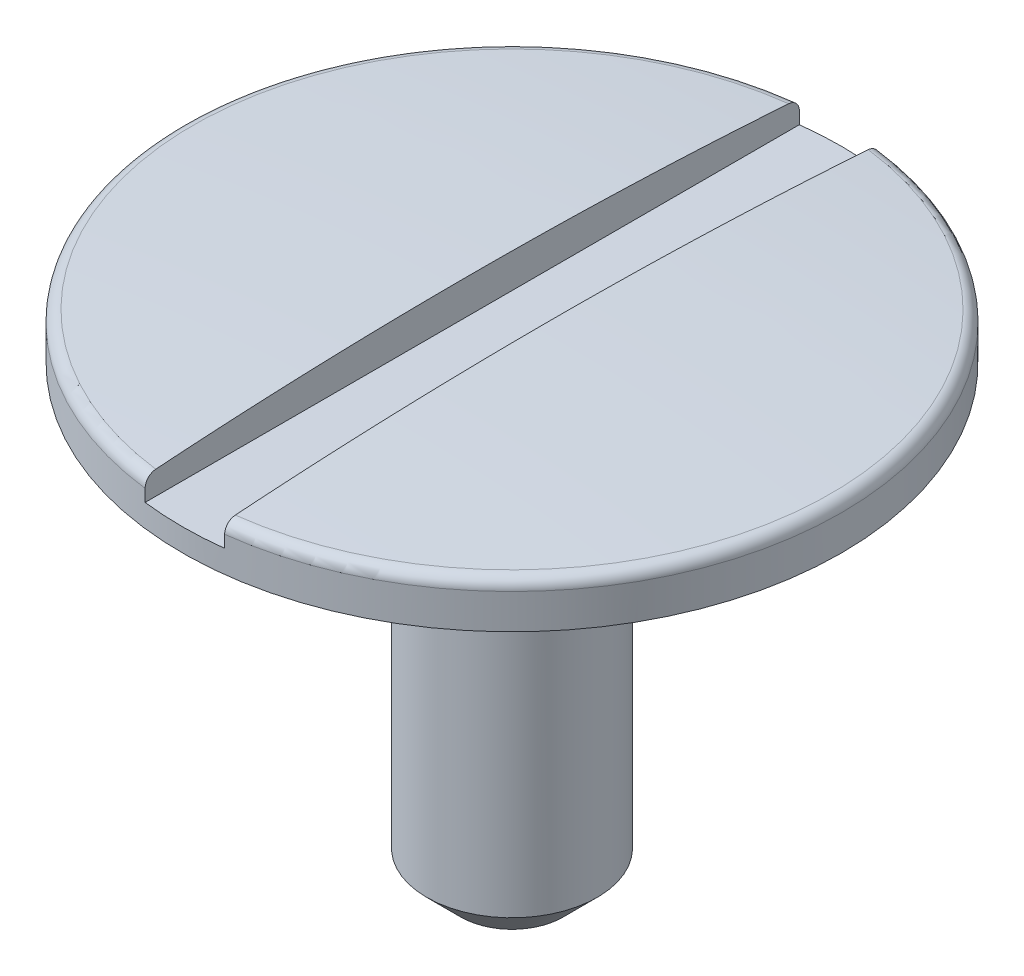
SolidWorks part; units mm, degrees
ref_plane "Alzado" through (0, 0, 0) normal (0, 0, 1) x (1, 0, 0)
ref_plane "Planta" through (0, 0, 0) normal (0, 1, 0) x (1, 0, 0)
ref_plane "Vista lateral" through (0, 0, 0) normal (1, 0, 0) x (0, 0, -1)
sketch "Sketch4" plane through (0, 0, 0) normal (0, 0, 1) x (1, 0, 0)
  line L0 (-848.3562, 0) -> (41569.4551, 0) construction
  line L1 (-848.2787, 0.2) -> (41569.5327, 0.2) construction
  line L2 (0, -848.3562) -> (0, 41569.4551) construction
  line L3 (1.45, -848.3562) -> (1.45, 41569.4551) construction
  line L4 (0, 0) -> (1.45, 0)
  line L5 (1.45, 0) -> (1.45, 0.2)
  line L6 (0, 0.2526) -> (0, 0)
  arc A1 (0, 0.2526) -> (1.45, 0.2) centre (0, -19.7474) cw
  point P8 (1.45, 0.2)
  dimension "D3" = 20
  dimension "D1" = 1.45
  dimension "D2" = 0.2
revolve "Revolve1" add sketch "Sketch4" angle 360 about L2
sketch "Sketch2" plane through (0, 0, 0) normal (0, 1, 0) x (1, 0, 0)
  circle A0 centre (0, 0) radius 0.375
  dimension "D1" = 0.75
extrude "Boss-Extrude2" add sketch "Sketch2" against normal blind 2
fillet "Fillet1" radius 0.05 1 edges at (1.45, 0.2, 0)
chamfer "Chamfer2" distance 0.15 angle 45 1 edges at (0, -2, 0.375)
sketch "Sketch3" plane through (0, 0, 0) normal (0, 0, 1) x (1, 0, 0)
  line L0 (0, -1000) -> (0, 49000) construction
  line L2 (-0.175, -999.9073) -> (-0.175, 49000.0927) construction
  line L3 (-1000, 0) -> (49000, 0) construction
  line L4 (-1000.8273, 0.1) -> (48999.1727, 0.1) construction
  line L5 (-0.175, 0.35) -> (0, 0.35)
  line L6 (-0.175, 0.35) -> (-0.175, 0.1)
  line L7 (0.175, 0.1) -> (0, 0.1)
  line L8 (-0.175, 0.1) -> (0, 0.1)
  line L9 (0.175, 0.35) -> (0.175, 0.1)
  line L10 (0.175, 0.35) -> (0, 0.35)
  dimension "D1" = 0.1
  dimension "D2" = 0.175
extrude "Cut-Extrude1" cut sketch "Sketch3" against normal through all both and the other way through all
